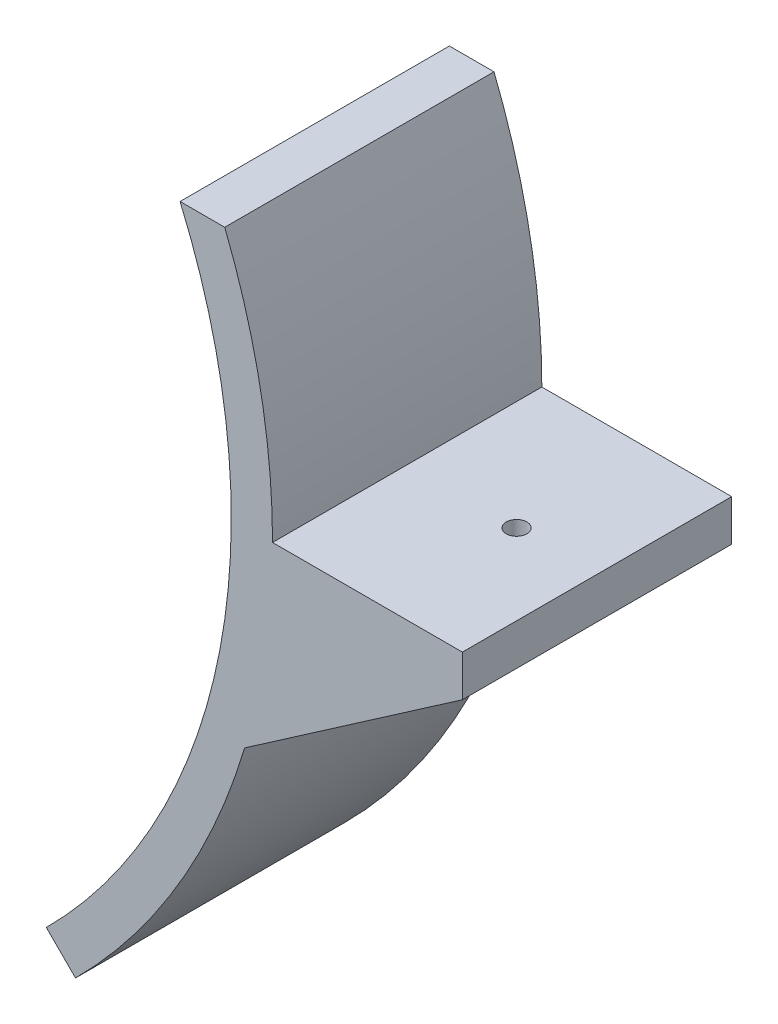
SolidWorks part; units mm, degrees
ref_plane "Alzado" through (0, 0, 0) normal (0, 0, 1) x (1, 0, 0)
ref_plane "Planta" through (0, 0, 0) normal (0, 1, 0) x (1, 0, 0)
ref_plane "Vista lateral" through (0, 0, 0) normal (1, 0, 0) x (0, 0, -1)
sketch "Croquis1" plane through (0, 0, 0) normal (0, 0, 1) x (1, 0, 0)
  line L0 (0, 0) -> (83.2684, 0)
  line L1 (163, 0) -> (209, 0)
  line L2 (209, 0) -> (209, -10)
  line L3 (209, -10) -> (156.2265, -46.5003)
  line L4 (0, 0) -> (115.2584, -115.2584)
  line L20 (151.4163, 60.3498) -> (140.5948, 60.3498)
  arc A1 (108.1873, -108.1873) -> (140.5948, 60.3498) centre (0, 0) ccw
  arc A2 (115.2584, -115.2584) -> (156.2265, -46.5003) centre (0, 0) ccw
  arc A5 (163, 0) -> (151.4163, 60.3498) centre (0, 0) ccw
  dimension "D1" = 45
extrude "Saliente-Extruir1" add sketch "Croquis1" along normal blind 65.25
sketch "Croquis3" plane through (209, 0, 0) normal (1, 0, 0) x (0, 0, -1)
  line L0 (0, 0) -> (-10, 0)
  line L1 (-65.25, 0) -> (0, 0) construction
  line L2 (-10, 0) -> (-10, -10)
  line L3 (-65.25, -10) -> (0, -10) construction
  line L4 (-10, -10) -> (0, -10)
  line L5 (0, -10) -> (0, 0)
  line L6 (-65.25, 0) -> (-55.25, 0)
  line L7 (-55.25, 0) -> (-55.25, -10)
  line L8 (-55.25, -10) -> (-65.25, -10)
  line L9 (-65.25, -10) -> (-65.25, 0)
  line L10 (-55.25, -10) -> (-65.25, -10)
  line L11 (-55.25, 0) -> (-10, 0)
  line L12 (-10, -10) -> (-55.25, -10)
  line L13 (-55.25, -10) -> (-55.25, -46.5003)
  line L14 (-65.25, -46.5003) -> (0, -46.5003) construction
  line L15 (-55.25, -46.5003) -> (-10, -46.5003)
  line L16 (-10, -46.5003) -> (-10, -10)
  line M4 (-65.25, -10) -> (0, -10)
extrude "Cortar-Extruir1" cut sketch "Croquis3" against normal blind 45 contours L15 L16 L13 M4
sketch "Croquis5" plane through (10, 0, 0) normal (1, 0, 0) x (0, 0, -1)
  circle A0 centre (-32.625, -172.8465) radius 2.5
  dimension "D1" = 5
extrude "Cortar-Extruir3" cut sketch "Croquis5" against normal blind 45
sketch "Croquis9" plane through (0, -10, 0) normal (0, -1, 0) x (-1, 0, 0)
  line L1 (-164, -10) -> (-164, -32.625)
  line L2 (-164, -55.25) -> (-164, -10) construction
  line L3 (-164, -55.25) -> (-164, -10)
  line L4 (-164, -10) -> (-164, -55.25) construction
  circle A0 centre (-189.5, -32.625) radius 2.5
  dimension "D1" = 25.5
extrude "Cortar-Extruir5" cut sketch "Croquis9" against normal blind 45 contours A0
